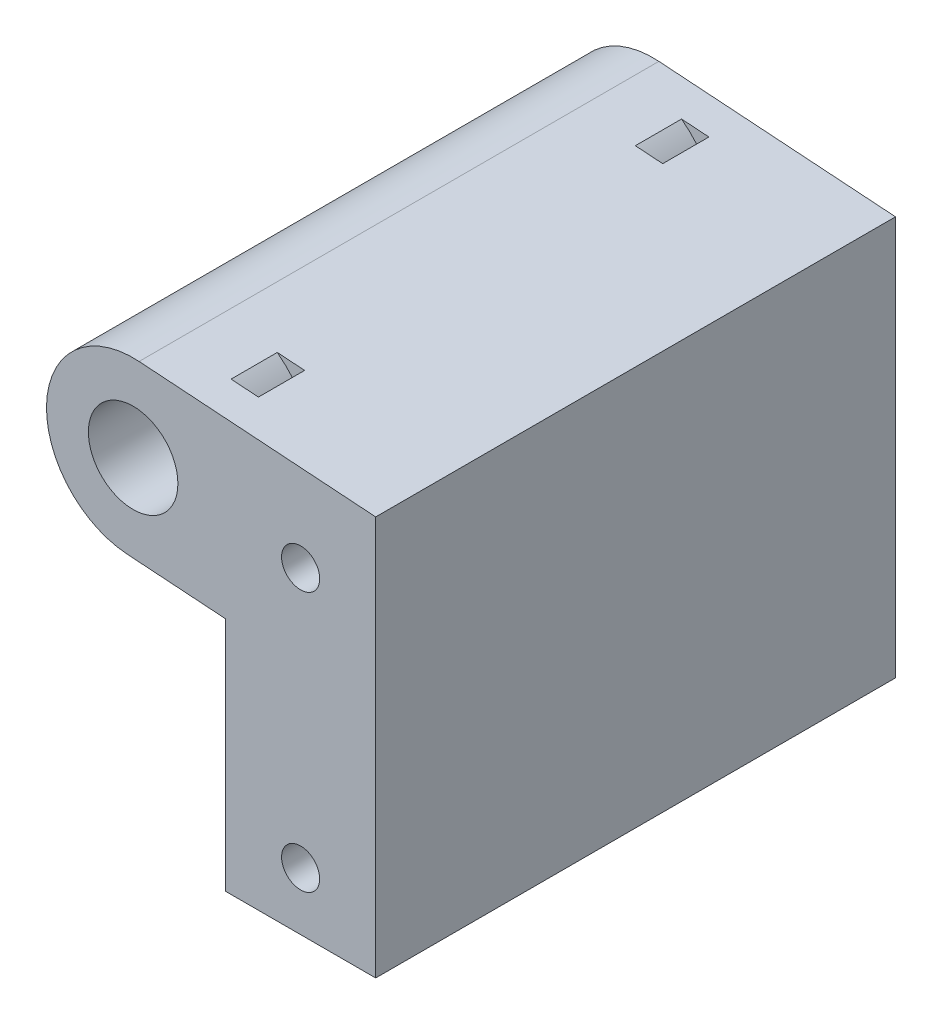
SolidWorks part; units mm, degrees
ref_plane "Front Plane" through (0, 0, 0) normal (0, 0, 1) x (1, 0, 0)
ref_plane "Top Plane" through (0, 0, 0) normal (0, 1, 0) x (1, 0, 0)
ref_plane "Right Plane" through (0, 0, 0) normal (1, 0, 0) x (0, 0, -1)
sketch "Sketch1" plane through (0, 0, 0) normal (0, 0, 1) x (1, 0, 0)
  line L0 (-182, 170) -> (-167.5, 169) construction
  line L1 (-167.5, 169) -> (-167.5, 146.5) construction
  line L2 (-182.516, 162.5178) -> (-174, 161.9305)
  line L3 (-174, 161.9305) -> (-174, 141.5)
  line L4 (-181.484, 177.4822) -> (-161, 176.0695)
  line L5 (-161, 176.0695) -> (-161, 141.5)
  line L6 (-174, 141.5) -> (-161, 141.5)
  line L7 (-167.5, 146.5) -> (-167.5, 141.5) construction
  circle A0 centre (-167.5, 146.5) radius 2.4 construction
  circle A3 centre (-167.5, 146.5) radius 2.4 construction
  circle A4 centre (-167.5, 169) radius 2.4 construction
  arc A5 (-182.516, 162.5178) -> (-181.484, 177.4822) centre (-182, 170) ccw
  dimension "D1" = 7.5
  dimension "D6" = 4.8
  dimension "D3" = 5
  dimension "D4" = 14.5
  dimension "D5" = 23.5
  dimension "D2" = 22.5
  dimension "D7" = 6.5
  dimension "D8" = 7.5
  dimension "D9" = 6.5
extrude "Boss-Extrude1" add sketch "Sketch1" along normal blind 45 contours L5 L6 L3 L2 A5 L4
sketch "Sketch2" plane through (0, 0, 0) normal (0, 0, -1) x (-1, 0, 0)
  line L0 (161, 176.0695) -> (181.484, 177.4822) construction
  line L2 (182.516, 162.5178) -> (174, 161.9305) construction
  arc A0 (176.5208, 177.1399) -> (177.5529, 162.1755) centre (182, 170) ccw
  arc A1 (181.484, 177.4822) -> (182.516, 162.5178) centre (182, 170) ccw construction
  arc A3 (175.6076, 178.3299) -> (176.8117, 160.8714) centre (182, 170) ccw
  arc A4 (176.5208, 177.1399) -> (175.6076, 178.3299) centre (176.0642, 177.7349) ccw
  arc A5 (177.5529, 162.1755) -> (176.8117, 160.8714) centre (177.1823, 161.5234) cw
  point P8 (177.508, 162.1724)
  point P9 (0, 0)
  point P10 (0, 0)
  point P11 (182.1468, 160.2513)
  point P17 (0, 0)
  dimension "D1" = 9
  dimension "D2" = 1.5
extrude "Cut-Extrude1" cut sketch "Sketch2" against normal mid plane 4 from offset 5 offset against normal yes
ref_plane "Plane1" through (0, 0, 22.5) normal (0, 0, -1) x (-1, 0, 0)
mirror "Mirror1" about plane through (0, 0, 22.5) normal (0, 0, -1) of "Cut-Extrude1"
hole_wizard "M4x0.7 Tapped Hole1" positions "Sketch3" profile "Sketch4" tap size "M4x0.7" standard "ANSI Metric" end condition through all
sketch "Sketch3" plane through (0, 0, 45) normal (0, 0, 1) x (1, 0, 0)
  point P0 (-167.5, 169)
  point P3 (-167.5, 146.5)
sketch "Sketch4" plane through (-167.5, 169, 45) normal (1, 0, 0) x (0, -1, 0)
  line L0 (0, 0) -> (0, 45)
  line L1 (0, 45) -> (1.65, 45)
  line L2 (1.65, 45) -> (1.65, 0)
  line L5 (1.65, 0) -> (0, 0)
  line L11 (0, -6.35) -> (0, 107.95) construction
  dimension "Thru Tap Drill Dia." = 3.3
  dimension "Thru Tap Drill Depth" = 45
cosmetic thread "Hole Thread1" parameters "D2"=4
cosmetic thread "Hole Thread2" parameters "D2"=4
sketch "Sketch5" plane through (0, 0, 45) normal (0, 0, 1) x (1, 0, 0)
  circle A0 centre (-182, 170) radius 7.5
extrude "Boss-Extrude2" add sketch "Sketch5" against normal through all
sketch "Sketch6" plane through (0, 0, 45) normal (0, 0, 1) x (1, 0, 0)
  circle A0 centre (-182, 170) radius 3.875
  dimension "D1" = 7.75
extrude "Cut-Extrude2" cut sketch "Sketch6" against normal through all
sketch "Sketch7" plane through (0, 0, 0) normal (0, 0, -1) x (-1, 0, 0)
  line L0 (181.4341, 177.4788) -> (182.4661, 162.5143)
  line L1 (181.4341, 177.4788) -> (181.5339, 177.4857)
  line L2 (182.4661, 162.5143) -> (182.5659, 162.5212)
  line L3 (181.5339, 177.4857) -> (182.5659, 162.5212)
  line L4 (161, 176.0695) -> (181.484, 177.4822) construction
  line L5 (182.516, 162.5178) -> (174, 161.9305) construction
  line L6 (182.516, 162.5178) -> (181.484, 177.4822) construction
  point P10 (181.484, 177.4822)
  dimension "D1" = 0.1
extrude "Cut-Extrude3" [suppressed] cut sketch "Sketch7" against normal through all
sketch "Sketch8" plane through (0, 0, 45) normal (0, 0, 1) x (1, 0, 0)
  line L0 (-182.5, 165) -> (-182.5, 175)
  line L1 (-182.5, 165) -> (-181.5, 165)
  line L2 (-182.5, 175) -> (-181.5, 175)
  line L3 (-181.5, 165) -> (-181.5, 175)
  line L4 (-182, 175) -> (-182, 165) construction
  line L5 (-182.5, 170) -> (-181.5, 170) construction
  line L6 (-185.8891, 166.818) -> (-178.818, 173.8891)
  line L7 (-185.8891, 166.818) -> (-185.182, 166.1109)
  line L8 (-178.818, 173.8891) -> (-178.1109, 173.182)
  line L9 (-185.182, 166.1109) -> (-178.1109, 173.182)
  line L10 (-178.4645, 173.5355) -> (-185.5355, 166.4645) construction
  line L11 (-182.3536, 170.3536) -> (-181.6464, 169.6464) construction
  line L12 (-187, 170.5) -> (-177, 170.5)
  line L13 (-187, 170.5) -> (-187, 169.5)
  line L14 (-177, 170.5) -> (-177, 169.5)
  line L15 (-187, 169.5) -> (-177, 169.5)
  line L16 (-177, 170) -> (-187, 170) construction
  line L17 (-182, 170.5) -> (-182, 169.5) construction
  line L18 (-185.182, 173.8891) -> (-178.1109, 166.818)
  line L19 (-185.182, 173.8891) -> (-185.8891, 173.182)
  line L20 (-178.1109, 166.818) -> (-178.818, 166.1109)
  line L21 (-185.8891, 173.182) -> (-178.818, 166.1109)
  line L22 (-178.4645, 166.4645) -> (-185.5355, 173.5355) construction
  line L23 (-181.6464, 170.3536) -> (-182.3536, 169.6464) construction
  circle A0 centre (-182, 170) radius 3.875 construction
  point P0 (-186.6989, 170)
  point P1 (-182, 170)
  point P3 (-182, 170)
  point P4 (-182, 170)
  point P7 (-182, 170)
  circle M21 centre (-182, 170) radius 3.875
  dimension "D1" = 45
  dimension "D2" = 1
  dimension "D3" = 10
extrude "Cut-Extrude4" [suppressed] cut sketch "Sketch8" against normal through all contours L21 L20 L18 M21 | L1 L3 L0 M21 | L7 L9 L6 M21 | L13 L15 L12 M21 | L19 L21 L18 M21 | L3 L2 L0 M21 | L9 L8 L6 M21 | L15 L14 L12 M21
ref_plane "Plane2" through (10.8071, 156.703, 0) normal (-0.0688, -0.9976, 0) x (-0.9976, 0.0688, 0)
sketch "Sketch9" plane through (10.8071, 156.703, 0) normal (-0.0688, -0.9976, 0) x (-0.9976, 0.0688, 0)
  line L0 (189.3901, 0) -> (189.3901, -45)
  line L1 (197.1401, -45) -> (197.1401, 0)
  line L2 (189.3901, -9) -> (187.8901, -12.5)
  line L3 (189.3901, -19) -> (189.3901, -26)
  line L4 (193.2651, 0) -> (193.2651, -45) construction
  line L5 (197.1401, 0) -> (189.3901, 0) construction
  line L6 (189.3901, -45) -> (197.1401, -45) construction
  line L7 (193.2651, -22.5) -> (187.8901, -22.5) construction
  line L8 (189.3901, -19) -> (187.8901, -22.5)
  line L9 (187.8901, -22.5) -> (189.3901, -26)
  line L10 (187.8901, -12.5) -> (189.3901, -16)
  line L11 (189.3901, -16) -> (189.3901, -9)
  line L12 (189.3901, -29) -> (189.3901, -36)
  line L13 (189.3901, -36) -> (187.8901, -32.5)
  line L15 (187.8901, -32.5) -> (189.3901, -29)
  point P19 (186.5719, -38)
  point P21 (187.8901, -34.9012)
  dimension "D1" = 1.5
  dimension "D2" = 7
  dimension "D3" = 10
  dimension "D4" = 10
revolve "Cut-Revolve1" cut sketch "Sketch9" angle 360 about L4
